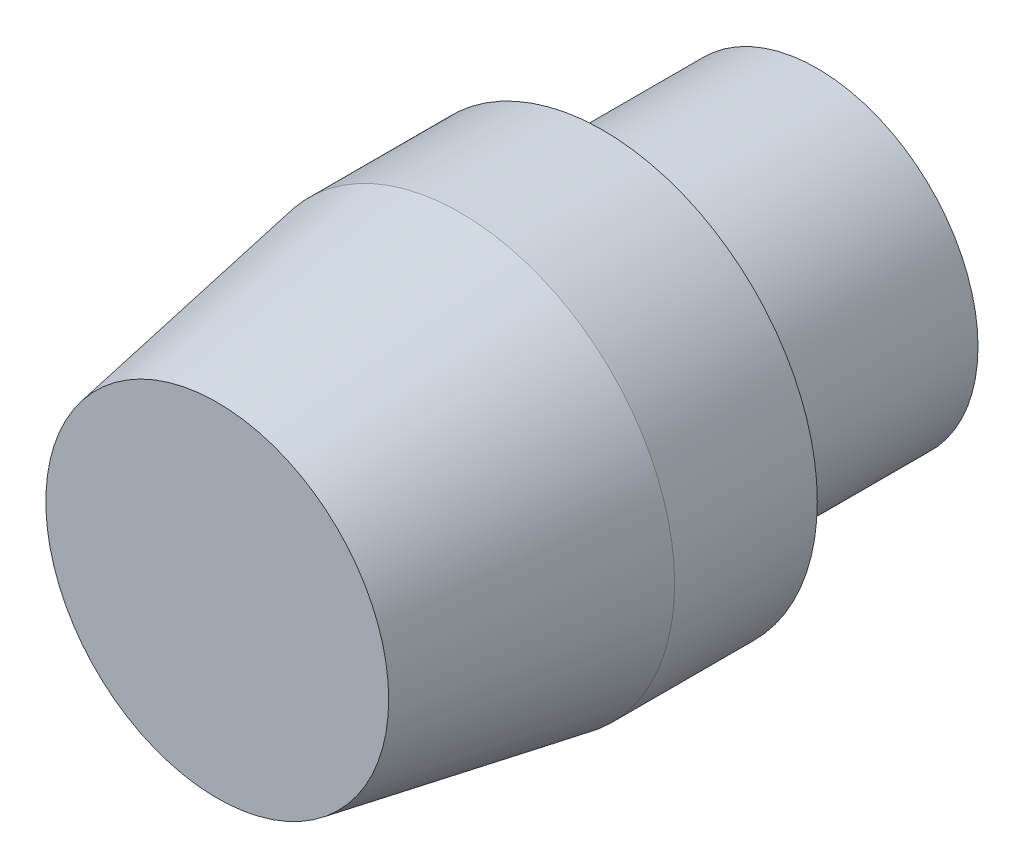
SolidWorks part; units mm, degrees
ref_plane "Front Plane" through (0, 0, 0) normal (0, 0, 1) x (1, 0, 0)
ref_plane "Top Plane" through (0, 0, 0) normal (0, 1, 0) x (1, 0, 0)
ref_plane "Right Plane" through (0, 0, 0) normal (1, 0, 0) x (0, 0, -1)
sketch "Sketch1" plane through (0, 0, 0) normal (0, 0, 1) x (1, 0, 0)
  circle A0 centre (0, 0) radius 7.5
extrude "Boss-Extrude1" add sketch "Sketch1" along normal blind 10
sketch "Sketch2" plane through (0, 0, 10) normal (0, 0, 1) x (1, 0, 0)
  circle A0 centre (0, 0) radius 10
extrude "Boss-Extrude2" add sketch "Sketch2" along normal blind 18
chamfer "Chamfer1" distance 2 angle 80 1 edges at (10, 0, 28)
